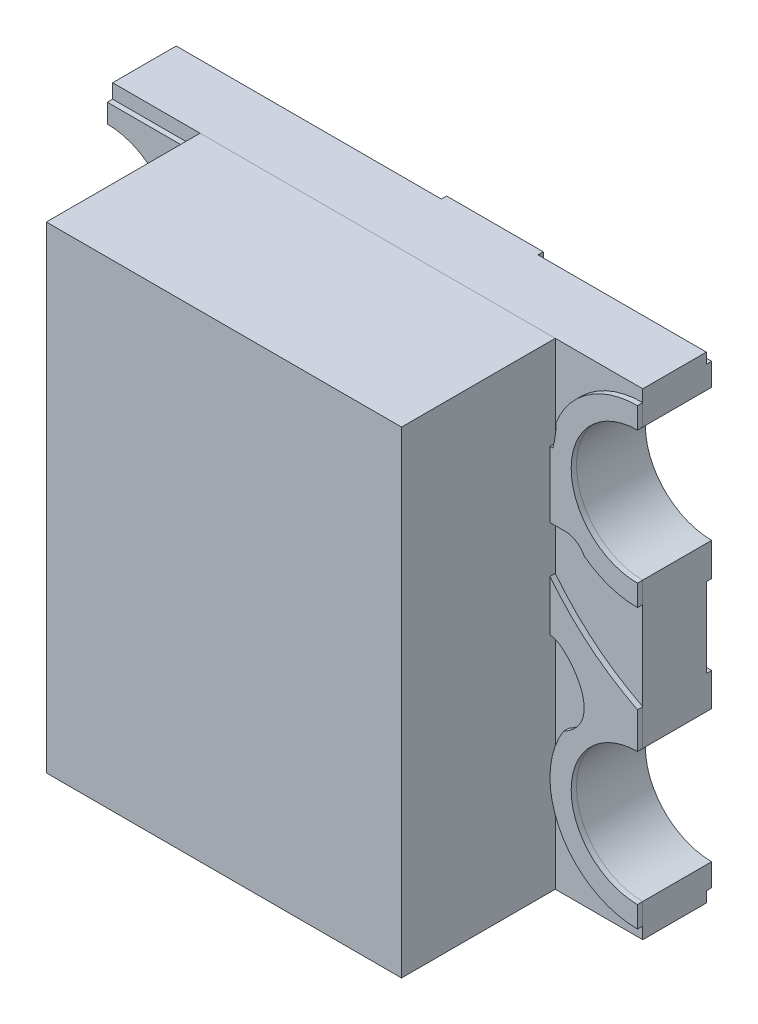
SolidWorks part; units mm, degrees
ref_plane "Front Plane" through (0, 0, 0) normal (0, 0, 1) x (1, 0, 0)
ref_plane "Top Plane" through (0, 0, 0) normal (0, 1, 0) x (1, 0, 0)
ref_plane "Right Plane" through (0, 0, 0) normal (1, 0, 0) x (0, 0, -1)
ref_plane "Plane1" through (0, 0, 0.02) normal (0, 0, -1) x (-1, 0, 0)
sketch "Sketch2" plane through (0, 0, 0.02) normal (0, 0, -1) x (-1, 0, 0)
  line L0 (0, 0.9) -> (0, -0.9) construction
  line L1 (1, -0.9) -> (-1, -0.9)
  line L2 (1, -0.9) -> (1, -0.775)
  line L3 (1, 0.9) -> (-1, 0.9)
  line L4 (-1, -0.9) -> (-1, -0.775)
  line L5 (1, -0.9) -> (-1, 0.9) construction
  line L6 (1, 0.9) -> (-1, -0.9) construction
  line L7 (-1, 0) -> (1, 0) construction
  line L8 (-1, 0.775) -> (-1, 0.9)
  line L9 (-1, -0.275) -> (-1, 0.275)
  line L10 (1, 0.775) -> (1, 0.9)
  line L11 (1, -0.275) -> (1, 0.275)
  arc A0 (-1, 0.275) -> (-1, 0.775) centre (-1, 0.525) ccw
  arc A1 (1, 0.275) -> (1, 0.775) centre (1, 0.525) cw
  arc A2 (1, -0.275) -> (1, -0.775) centre (1, -0.525) ccw
  arc A3 (-1, -0.275) -> (-1, -0.775) centre (-1, -0.525) cw
  point P0 (0, 0)
  dimension "D4" = 0.25
  dimension "D1" = 2
  dimension "D2" = 1.8
  dimension "D3" = 0.375
  dimension "D5" = 0.375
extrude "Boss-Extrude1" add sketch "Sketch2" against normal blind 0.24
sketch "Sketch3" plane through (0, 0, 0.02) normal (0, 0, -1) x (-1, 0, 0)
  line L0 (-1, 0.275) -> (-1, 0.15)
  line L1 (-1, 0.15) -> (-0.53, 0.15)
  line L3 (-1, 0.86) -> (-0.53, 0.86)
  line L4 (-0.53, 0.15) -> (-0.53, 0.86)
  line L5 (-1, 0.15) -> (-0.53, 0.86) construction
  line L6 (-1, 0.86) -> (-0.53, 0.15) construction
  line L7 (0, 0) -> (-1, 0) construction
  line L8 (-1, 0.275) -> (-1, -0.275) construction
  line L9 (1, 0.9) -> (-1, 0.9) construction
  line L10 (0.53, 0.15) -> (0.53, 0.86)
  line L11 (1, 0.15) -> (0.53, 0.15)
  line L12 (1, 0.275) -> (1, 0.15)
  line L13 (1, 0.775) -> (1, 0.86)
  line L14 (1, 0.86) -> (0.53, 0.86)
  line L15 (0, 0) -> (0, 0.9) construction
  line L16 (-1, 0.775) -> (-1, 0.86)
  line L17 (-1, -0.86) -> (-0.53, -0.15) construction
  line L18 (-1, -0.15) -> (-0.53, -0.86) construction
  line L19 (-1, -0.775) -> (-1, -0.86)
  line L20 (1, -0.86) -> (0.53, -0.86)
  line L21 (1, -0.775) -> (1, -0.86)
  line L22 (1, -0.275) -> (1, -0.15)
  line L23 (1, -0.15) -> (0.53, -0.15)
  line L24 (0.53, -0.15) -> (0.53, -0.86)
  line L25 (-0.53, -0.15) -> (-0.53, -0.86)
  line L26 (-1, -0.86) -> (-0.53, -0.86)
  line L28 (-1, -0.15) -> (-0.53, -0.15)
  line L29 (-1, -0.275) -> (-1, -0.15)
  line L30 (-1, -0.9) -> (1, -0.9) construction
  line L31 (-0.3649, -0.9) -> (0, -0.9)
  line L32 (-0.3649, -0.9) -> (-0.3649, 0.9)
  line L33 (-0.3649, 0.9) -> (0, 0.9)
  line L34 (0, -0.9) -> (0, 0.9)
  arc A0 (1, 0.275) -> (1, 0.775) centre (1, 0.525) cw
  arc A1 (-1, -0.275) -> (-1, -0.775) centre (-1, -0.525) cw
  arc A2 (-1, 0.275) -> (-1, 0.775) centre (-1, 0.525) ccw
  arc A3 (-1, 0.275) -> (-1, 0.775) centre (-1, 0.525) ccw
  arc A4 (1, -0.275) -> (1, -0.775) centre (1, -0.525) ccw
  point P0 (-0.765, 0.505)
  point P39 (-0.765, -0.505)
  line M6 (-1, 0.9) -> (-1, 0.775)
  arc M7 (-1, 0.775) -> (-1, 0.275) centre (-1, 0.525) cw
  line M8 (-1, 0.275) -> (-1, -0.275)
  arc M9 (-1, -0.275) -> (-1, -0.775) centre (-1, -0.525) cw
  line M10 (-1, -0.775) -> (-1, -0.9)
  line M11 (-1, -0.9) -> (1, -0.9)
  line M12 (1, -0.9) -> (1, -0.775)
  arc M13 (1, -0.775) -> (1, -0.275) centre (1, -0.525) cw
  line M14 (1, -0.275) -> (1, 0.275)
  arc M15 (1, 0.275) -> (1, 0.775) centre (1, 0.525) cw
  line M16 (1, 0.775) -> (1, 0.9)
  line M17 (1, 0.9) -> (-1, 0.9)
  dimension "D1" = 0.47
  dimension "D2" = 0.15
  dimension "D4" = 0.71
  dimension "D5" = 0
extrude "Boss-Extrude2" add sketch "Sketch3" along normal blind 0.02 contours L1 L4 L3 M6 M7 M8 | L14 L10 L11 M16 M14 M15 | L23 L24 L20 M12 M13 M14 | L28 L26 L25 M8 M9 M10 | L34 L32 M11 M17
sketch "Sketch4" plane through (0, 0, 0.26) normal (0, 0, 1) x (1, 0, 0)
  line L0 (71.5675, 201.9477) -> (362.2342, 201.9477) construction
  line L1 (-1, -0.275) -> (-1, 0.275) construction
  line L2 (-1, 0.775) -> (-1, 0.9) construction
  line L3 (-0.5389, 0.8464) -> (0.3901, 0.8464)
  line L4 (0.3901, 0.8464) -> (0.3901, 0.6856)
  line L5 (0.3901, 0.6856) -> (-0.6767, 0.6856)
  line L6 (1, -0.855) -> (1, -0.775)
  line L7 (-1, 0.8464) -> (-1, 0.775)
  line L8 (-1, -0.9) -> (-1, -0.775) construction
  line L9 (-1, 0.275) -> (-1, 0.1864)
  line L10 (-1, -0.195) -> (-1, -0.275)
  line L11 (-0.6035, -0.2066) -> (0.5359, -0.2066)
  line L12 (-1, -0.775) -> (-1, -0.855)
  line L13 (0.5359, -0.2066) -> (0.5359, -0.7671)
  line L14 (1, 0.275) -> (1, -0.275) construction
  line L15 (1, -0.775) -> (1, -0.9) construction
  line L16 (0.636, 0.1776) -> (0.5359, 0.1776)
  line L17 (0.5359, -0.7671) -> (-0.5741, -0.7671)
  line L18 (-0.5741, -0.7671) -> (-0.5741, -0.685)
  line L19 (-0.6111, -0.6073) -> (-0.6767, -0.5541)
  line L20 (0.5359, 0.1776) -> (0.5359, -0.0571)
  line L21 (0.5359, -0.0571) -> (0.6535, -0.0571)
  line L22 (1, -0.275) -> (1, -0.1386)
  line L23 (1, 0.9) -> (1, 0.775) construction
  line L24 (0.4124, 0.2081) -> (0.4124, 0.0429)
  line L25 (0.3124, -0.0571) -> (-0.5035, -0.0571)
  line L26 (-0.6035, 0.0429) -> (-0.6035, 0.4569)
  line L27 (-0.5035, 0.5569) -> (0.6809, 0.5569)
  line L28 (0.5124, 0.3081) -> (0.7175, 0.3081)
  line L29 (-0.6788, -0.6007) -> (-0.6767, -0.5541)
  arc A0 (-1, 0.1864) -> (-0.6995, 0.6528) centre (-1, 0.5164) ccw
  arc A2 (-1, 0.1864) -> (-0.712, 0.6775) centre (-1, 0.5164) ccw
  arc A3 (-1, 0.275) -> (-1, 0.775) centre (-1, 0.525) ccw
  arc A4 (-1, 0.275) -> (-1, 0.775) centre (-1, 0.525) ccw
  arc A5 (-1, -0.195) -> (-0.8333, -0.2402) centre (-1, -0.525) cw
  arc A6 (-0.6788, -0.6007) -> (-1, -0.855) centre (-1, -0.525) cw
  arc A7 (-1, -0.775) -> (-1, -0.275) centre (-1, -0.525) ccw
  arc A8 (-1, -0.775) -> (-1, -0.275) centre (-1, -0.525) ccw
  arc A9 (-0.5741, -0.685) -> (-0.6111, -0.6073) centre (-0.6741, -0.685) ccw
  arc A10 (-0.6035, -0.2066) -> (-0.6635, -0.2265) centre (-0.6035, -0.3066) ccw
  arc A11 (0.7212, -0.3484) -> (1, -0.855) centre (1, -0.525) ccw
  arc A12 (0.6535, -0.0571) -> (0.7175, -0.0803) centre (0.6535, -0.1571) cw
  arc A13 (1, 0.195) -> (0.7998, 0.2627) centre (1, 0.525) cw
  arc A14 (1, 0.775) -> (1, 0.275) centre (1, 0.525) ccw
  arc A15 (1, -0.275) -> (1, -0.775) centre (1, -0.525) ccw
  arc A16 (1, -0.275) -> (1, -0.775) centre (1, -0.525) ccw
  arc A17 (1, 0.775) -> (1, 0.275) centre (1, 0.525) ccw
  arc A18 (0.6932, 0.6465) -> (1, 0.855) centre (1, 0.525) cw
  arc A19 (-0.6035, 0.4569) -> (-0.5035, 0.5569) centre (-0.5035, 0.4569) cw
  arc A20 (-0.5035, -0.0571) -> (-0.6035, 0.0429) centre (-0.5035, 0.0429) cw
  arc A21 (0.4124, 0.0429) -> (0.3124, -0.0571) centre (0.3124, 0.0429) cw
  arc A22 (0.4124, 0.2081) -> (0.5124, 0.3081) centre (0.5124, 0.2081) cw
  spline S0 degree 1 poles (-0.5389, 0.8464) (-0.6907, 0.8464) knots 0 0 1 1
  spline S1 degree 2 poles (-0.6907, 0.8464) (-0.8453, 0.8464) (-1, 0.8464) knots 0 0 0 1 1 1
  spline S2 degree 3 poles (-0.6635, -0.2265) (-0.6893, -0.2458) (-0.7255, -0.2513) (-0.8008, -0.2607) (-0.8333, -0.2402) knots 0.089776 0.089776 0.089776 0.089776 0.400477 1 1 1 1
  spline S4 degree 2 poles (1, -0.1386) (0.7798, -0.027) (0.636, 0.1776) knots 0 0 0 1 1 1
  spline S5 degree 3 poles (0.7175, -0.0803) (0.7859, -0.1372) (0.8586, -0.274) (0.7212, -0.3484) knots 0.124405 0.124405 0.124405 0.124405 1 1 1 1
  spline S6 degree 2 poles (0.6809, 0.5569) (0.6929, 0.6009) (0.6932, 0.6465) knots 0 0 0 1 1 1
  spline S7 degree 2 poles (0.7175, 0.3081) (0.7712, 0.3118) (0.7998, 0.2627) knots 0 0 0 1 1 1
  spline S8 degree 2 poles (-0.6767, 0.6856) (-0.6942, 0.6807) (-0.712, 0.6775) knots 0 0 0 1 1 1
  dimension "D3" = 0.1
  dimension "D4" = 0.1
  dimension "D7" = 0.1
  dimension "D8" = 0.33
  dimension "D9" = 0.33
  dimension "D10" = 0.33
  dimension "D11" = 0.33
  dimension "D1" = 0
  dimension "D2" = 0
  dimension "D5" = 0
  dimension "D6" = 0
extrude "Boss-Extrude3" add sketch "Sketch4" along normal blind 0.02 separate body
sketch "Sketch5" plane through (0, 0, 0.26) normal (0, 0, 1) x (1, 0, 0)
  line L1 (-0.4343, 0.451) -> (0.3196, 0.451)
  line L2 (-0.4343, 0.451) -> (-0.4343, 0.0404)
  line L3 (-0.4343, 0.0404) -> (0.3196, 0.0404)
  line L4 (0.3196, 0.451) -> (0.3196, 0.0404)
  line L5 (-0.1178, -0.3594) -> (0.0558, -0.3594)
  line L6 (-0.1178, -0.3594) -> (-0.1178, -0.5316)
  line L7 (-0.1178, -0.5316) -> (0.0558, -0.5316)
  line L8 (0.0558, -0.3594) -> (0.0558, -0.5316)
  line L9 (-0.4135, -0.3594) -> (-0.3096, -0.3594)
  line L10 (-0.4135, -0.3594) -> (-0.4135, -0.5316)
  line L11 (-0.4135, -0.5316) -> (-0.3096, -0.5316)
  line L12 (-0.3096, -0.3594) -> (-0.3096, -0.5316)
  line L13 (0.2532, -0.3594) -> (0.3433, -0.3594)
  line L14 (0.2532, -0.3594) -> (0.2532, -0.5316)
  line L15 (0.2532, -0.5316) -> (0.3433, -0.5316)
  line L16 (0.3433, -0.3594) -> (0.3433, -0.5316)
extrude "Boss-Extrude4" add sketch "Sketch5" along normal blind 0.021 separate body
sketch "Sketch6" plane through (0, 0, 0.26) normal (0, 0, 1) x (1, 0, 0)
  line L0 (-1, 0.9) -> (1, 0.9) construction
  line L1 (0.67, -0.9) -> (-0.67, -0.9)
  line L2 (0.67, -0.9) -> (0.67, 0.9)
  line L3 (0.67, 0.9) -> (-0.67, 0.9)
  line L4 (-0.67, -0.9) -> (-0.67, 0.9)
  line L5 (0.67, -0.9) -> (-0.67, 0.9) construction
  line L6 (0.67, 0.9) -> (-0.67, -0.9) construction
  point P0 (0, 0)
  dimension "D1" = 1.34
extrude "Boss-Extrude5" add sketch "Sketch6" along normal blind 0.58 separate body
